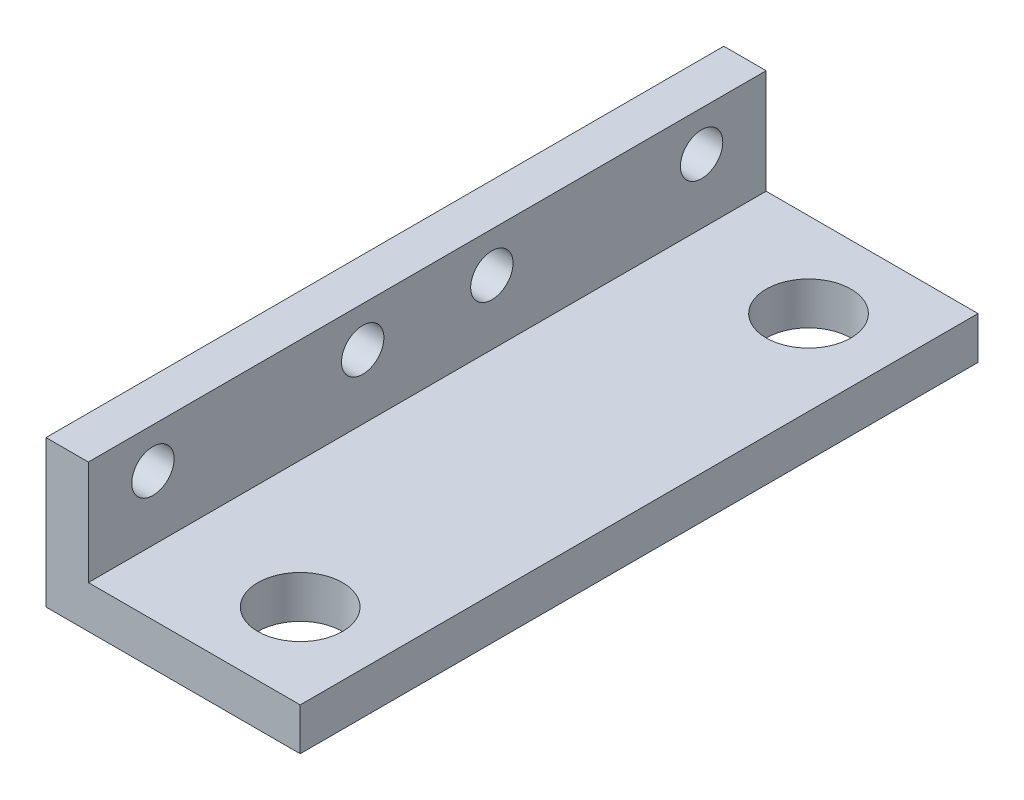
SolidWorks part; units mm, degrees
material "1060 Alloy"
ref_plane "Front Plane" through (0, 0, 0) normal (0, 0, 1) x (1, 0, 0)
ref_plane "Top Plane" through (0, 0, 0) normal (0, 1, 0) x (1, 0, 0)
ref_plane "Right Plane" through (0, 0, 0) normal (1, 0, 0) x (0, 0, -1)
sketch "Sketch1" plane through (0, 0, 0) normal (0, 0, 1) x (1, 0, 0)
  line L0 (0, 0) -> (0, 11)
  line L1 (0, 11) -> (3.175, 11)
  line L2 (3.175, 11) -> (3.175, 3.175)
  line L3 (3.175, 3.175) -> (19.05, 3.175)
  line L4 (19.05, 3.175) -> (19.05, 0)
  line L5 (19.05, 0) -> (0, 0)
  dimension "D1" = 11
  dimension "D2" = 19.05
  dimension "D3" = 3.175
  dimension "D4" = 3.175
extrude "Boss-Extrude1" add sketch "Sketch1" along normal blind 50.8
sketch "Sketch2" plane through (3.175, 0, 0) normal (1, 0, 0) x (0, 0, -1)
  line L0 (-45.96, 8) -> (-4.84, 8) construction
  line L3 (-25.4, 11) -> (-25.4, 3.175) construction
  line L5 (-50.8, 11) -> (0, 11) construction
  line L6 (-50.8, 3.175) -> (0, 3.175) construction
  circle A0 centre (-45.96, 8) radius 1.5875
  circle A1 centre (-30.24, 8) radius 1.5875
  circle A2 centre (-20.56, 8) radius 1.5875
  circle A3 centre (-4.84, 8) radius 1.5875
  point P0 (-25.4, 8)
  dimension "D2" = 3.175
  dimension "D3" = 3.175
  dimension "D4" = 3.175
  dimension "D5" = 3.175
  dimension "D6" = 15.72
  dimension "D7" = 15.72
  dimension "D8" = 9.68
extrude "Cut-Extrude1" cut sketch "Sketch2" against normal blind 10
sketch "Sketch5" plane through (0, 3.175, 0) normal (0, 1, 0) x (1, 0, 0)
  line L0 (12.7, 0) -> (12.7, -50.8) construction
  line L1 (19.05, 0) -> (3.175, 0) construction
  line L2 (19.05, -50.8) -> (3.175, -50.8) construction
  line L5 (3.175, -50.8) -> (3.175, 0) construction
  circle A0 centre (12.7, -6.35) radius 3.175
  circle A1 centre (12.7, -44.45) radius 3.175
  dimension "D1" = 6.35
  dimension "D2" = 6.35
  dimension "D3" = 9.525
  dimension "D4" = 38.1
  dimension "D5" = 6.35
extrude "Cut-Extrude2" cut sketch "Sketch5" against normal blind 6.35
